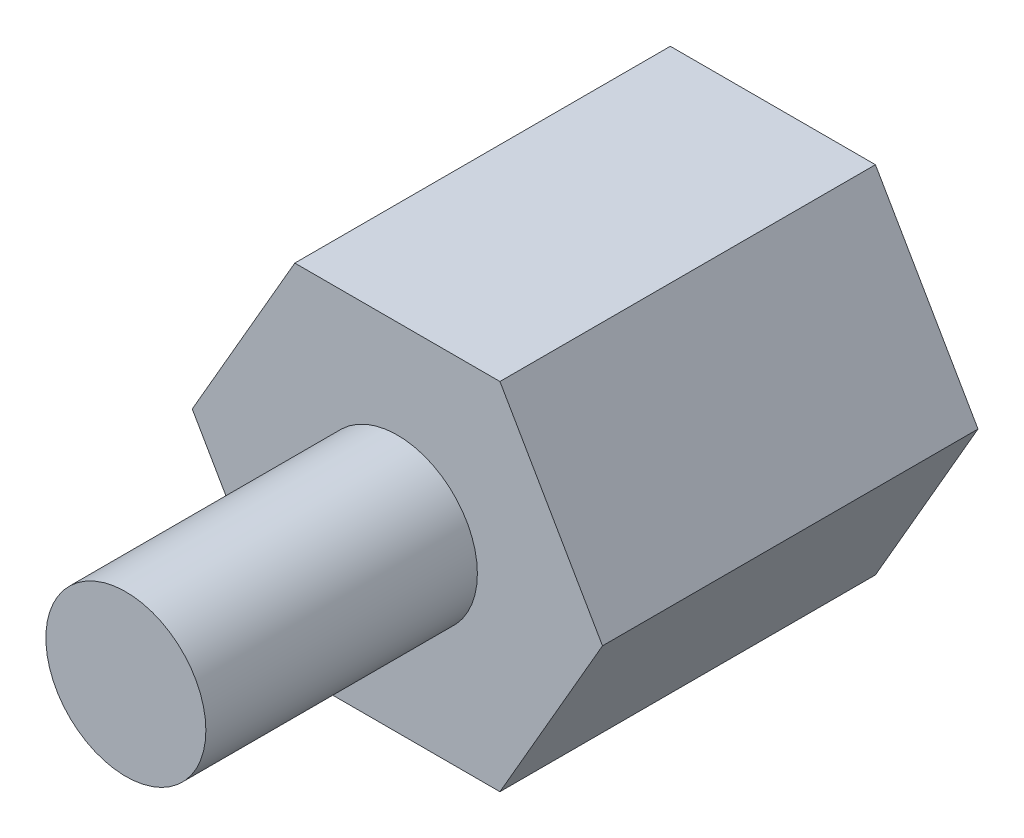
SolidWorks part; units mm, degrees
ref_plane "Plan de face" through (0, 0, 0) normal (0, 0, 1) x (1, 0, 0)
ref_plane "Plan de dessus" through (0, 0, 0) normal (0, 1, 0) x (1, 0, 0)
ref_plane "Plan de droite" through (0, 0, 0) normal (1, 0, 0) x (0, 0, -1)
sketch "Esquisse1" plane through (0, 0, 0) normal (0, 0, 1) x (1, 0, 0)
  line L1 (3.5507, 0) -> (1.7754, 3.075)
  line L2 (1.7754, 3.075) -> (-1.7754, 3.075)
  line L3 (-1.7754, 3.075) -> (-3.5507, 0)
  line L4 (-3.5507, 0) -> (-1.7754, -3.075)
  line L5 (-1.7754, -3.075) -> (1.7754, -3.075)
  line L6 (1.7754, -3.075) -> (3.5507, 0)
  circle A0 centre (0, 0) radius 3.075 construction
extrude "Boss.-Extru.1" add sketch "Esquisse1" along normal blind 6.5
sketch "Esquisse2" plane through (0, 0, 6.5) normal (0, 0, 1) x (1, 0, 0)
  circle A0 centre (0, 0) radius 1.385
extrude "Boss.-Extru.2" add sketch "Esquisse2" along normal blind 4.7
sketch "Esquisse3" plane through (0, 0, 0) normal (0, 0, -1) x (-1, 0, 0)
  circle A0 centre (0, 0) radius 1.35
extrude "Enlèv. mat.-Extru.1" cut sketch "Esquisse3" against normal blind 4.7
